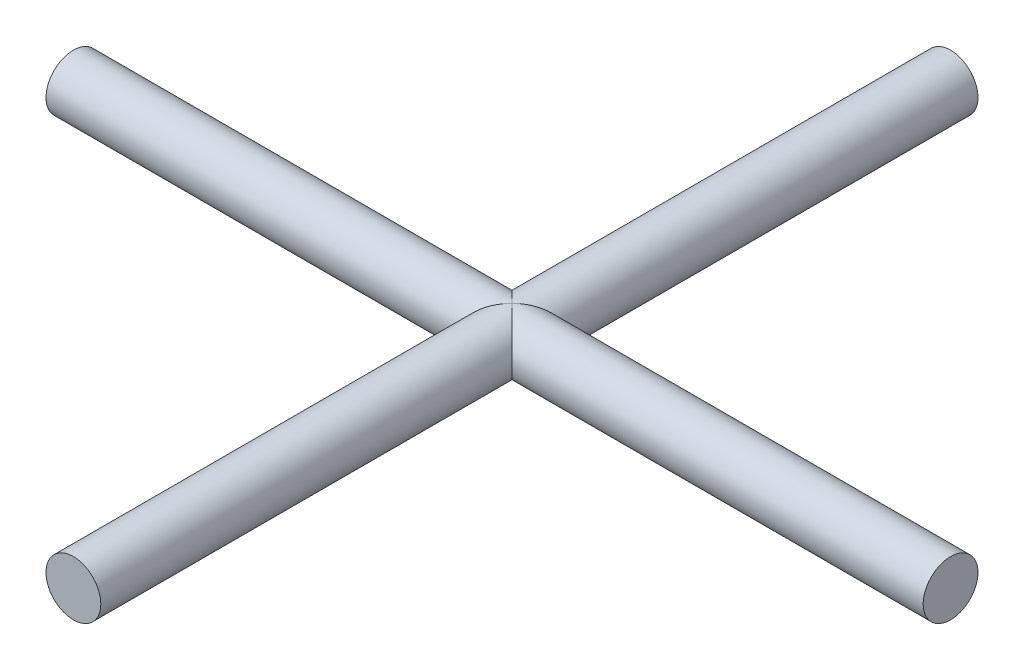
SolidWorks part; units mm, degrees
ref_plane "Front Plane" through (0, 0, 0) normal (0, 0, 1) x (1, 0, 0)
ref_plane "Top Plane" through (0, 0, 0) normal (0, 1, 0) x (1, 0, 0)
ref_plane "Right Plane" through (0, 0, 0) normal (1, 0, 0) x (0, 0, -1)
sketch "Sketch4" plane through (0, 0, 0) normal (0, 0, 1) x (1, 0, 0)
  circle A0 centre (0, 0) radius 2.5
extrude "Boss-Extrude3" add sketch "Sketch4" along normal mid plane 80
sketch "Sketch5" plane through (0, 0, 0) normal (1, 0, 0) x (0, 0, -1)
  circle A0 centre (0, 0) radius 2.5
extrude "Boss-Extrude4" add sketch "Sketch5" along normal mid plane 80
